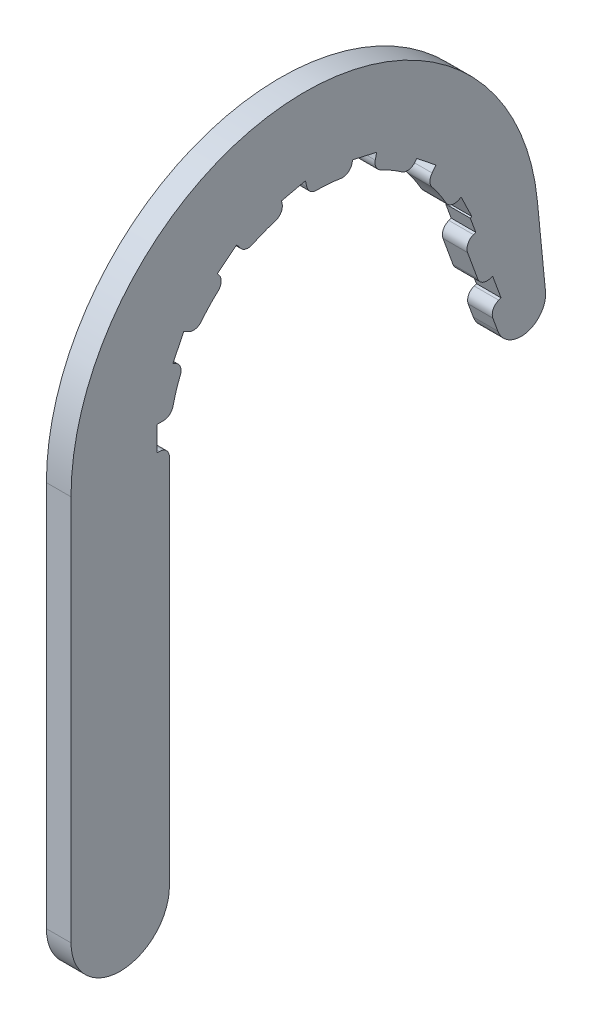
SolidWorks part; units mm, degrees
material "1060 Alloy"
ref_plane "Front Plane" through (0, 0, 0) normal (0, 0, 1) x (1, 0, 0)
ref_plane "Top Plane" through (0, 0, 0) normal (0, 1, 0) x (1, 0, 0)
ref_plane "Right Plane" through (0, 0, 0) normal (1, 0, 0) x (0, 0, -1)
sketch "Sketch1" plane through (0, 0, 0) normal (1, 0, 0) x (0, 0, -1)
  line L0 (-63.5, -98.425) -> (-63.5, 1.27)
  line L2 (-38.1, 0) -> (-38.1, -98.425)
  line L8 (56.8592, 7.1859) -> (58.9479, -14.0097)
  line L10 (46.6614, -16.8043) -> (35.8023, 13.031)
  arc A0 (56.8592, 7.1859) -> (-63.5, 1.27) centre (-3.175, 1.27) ccw
  arc A2 (35.8023, 13.031) -> (-38.1, 0) centre (0, 0) ccw
  arc A4 (46.6614, -16.8043) -> (58.9479, -14.0097) centre (52.6285, -14.6324) ccw
  arc A5 (-38.1, -98.425) -> (-63.5, -98.425) centre (-50.8, -98.425) cw
  dimension "D1" = 38.1
  dimension "D8" = 1.27
  dimension "D11" = 6.35
  dimension "D3" = 98.425
  dimension "D2" = 25.4
  dimension "D4" = 20
  dimension "D7" = 3.175
  dimension "D9" = 31.75
extrude "Boss-Extrude1" add sketch "Sketch1" along normal blind 6.35
sketch "Sketch4" plane through (6.35, 0, 0) normal (1, 0, 0) x (0, 0, -1)
  line L0 (44.4896, -10.8372) -> (47.4731, -9.7513)
  line L1 (47.4731, -9.7513) -> (45.3013, -3.7843)
  line L2 (45.3013, -3.7843) -> (42.3178, -4.8702)
  line L3 (35.8023, 13.031) -> (46.6614, -16.8043) construction
  line L4 (42.3178, -4.8702) -> (44.4896, -10.8372)
  line L5 (35.8023, 13.031) -> (46.6614, -16.8043) construction
  dimension "D1" = 6.35
  dimension "D2" = 3.175
  dimension "D3" = 6.35
sketch "Sketch5" plane through (6.35, 0, 0) normal (1, 0, 0) x (0, 0, -1)
  line L0 (-38.1, -98.425) -> (-38.1, 0) construction
  line L1 (-38.1, 0) -> (-41.275, 0)
  line L3 (-38.1, 6.35) -> (-41.275, 6.35)
  line L4 (-41.275, 0) -> (-41.275, 6.35)
  line L5 (-38.1, 6.35) -> (-35.0617, 6.35)
  line L6 (-35.0617, 6.35) -> (-35.0617, 0)
  line L7 (-35.0617, 0) -> (-38.1, 0)
  arc A0 (35.8023, 13.031) -> (-38.1, 0) centre (0, 0) ccw construction
  dimension "D1" = 6.35
  dimension "D2" = 3.175
sketch "Sketch6" plane through (0, 0, 0) normal (1, 0, 0) x (0, 0, -1)
  line L1 (-25.4, -44.014) -> (25.4, -44.014) construction
  line L2 (-25.4, -44.014) -> (-25.4, 6.786) construction
  line L3 (-25.4, 6.786) -> (25.4, 6.786) construction
  line L4 (25.4, -44.014) -> (25.4, 6.786) construction
  line L5 (-25.4, -44.014) -> (25.4, 6.786) construction
  line L6 (-25.4, 6.786) -> (25.4, -44.014) construction
  point P0 (0, -18.614)
  dimension "D1" = 50.8
  dimension "D2" = 50.8
extrude "Cut-Extrude1" cut sketch "Sketch4" against normal through all both and the other way through all
pattern_linear "LPattern1" count 2 spacing 19.05 along (0, 0.9397, 0.342) of "Cut-Extrude1"
extrude "Cut-Extrude2" cut sketch "Sketch5" against normal through all both and the other way through all
pattern_circular "CirPattern2" count 8 over 180 about axis through (0, 0, 0) along (1, 0, 0) skipping 7 of "Cut-Extrude2"
fillet "Fillet1" radius 2.54 16 edges at (3.175, 0, 38.1) (3.175, 6.35, 37.5671) (3.175, 16.531, 34.3269) (3.175, 22.0209, 31.0916) (3.175, 29.7878, 23.755) (3.175, 33.3303, 18.4581) (3.175, 37.1448, 8.478) (3.175, 38.0382, 2.1687) (3.175, 37.1448, -8.478) (3.175, 35.2122, -14.5503) (3.175, 29.7878, -23.755) (3.175, 25.412, -28.3873) (3.175, 16.531, -34.3269) (3.175, 7.0639, -37.9741) (3.175, -10.8372, -44.4896) (3.175, -4.8702, -42.3178)
